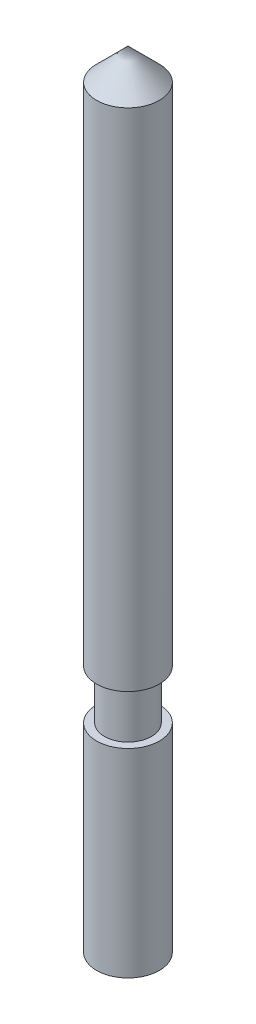
SolidWorks part; units mm, degrees
ref_plane "Спереди" through (0, 0, 0) normal (0, 0, 1) x (1, 0, 0)
ref_plane "Сверху" through (0, 0, 0) normal (0, 1, 0) x (1, 0, 0)
ref_plane "Справа" through (0, 0, 0) normal (1, 0, 0) x (0, 0, -1)
sketch "Эскиз1" plane through (0, 0, 0) normal (0, 0, 1) x (1, 0, 0)
  line L0 (0, 20.7326) -> (0, -20.0866) construction
  line L1 (0, 14.6397) -> (-1, 13.6397)
  line L2 (-1, 13.6397) -> (-1, -2.4603)
  line L3 (-1, -2.4603) -> (-0.75, -2.4603)
  line L4 (-0.75, -2.4603) -> (-0.75, -4.0303)
  line L5 (-0.75, -4.0303) -> (-1, -4.0303)
  line L6 (-1, -4.0303) -> (-1, -10.3603)
  line L7 (-1, -10.3603) -> (0, -10.3603)
  line L8 (0, -10.3603) -> (0, 14.6397)
  dimension "D1" = 1
  dimension "D2" = 6.33
  dimension "D3" = 25
  dimension "D4" = 7.9
  dimension "D5" = 0.75
revolve "Повернуть1" add sketch "Эскиз1" angle 360 about L0
